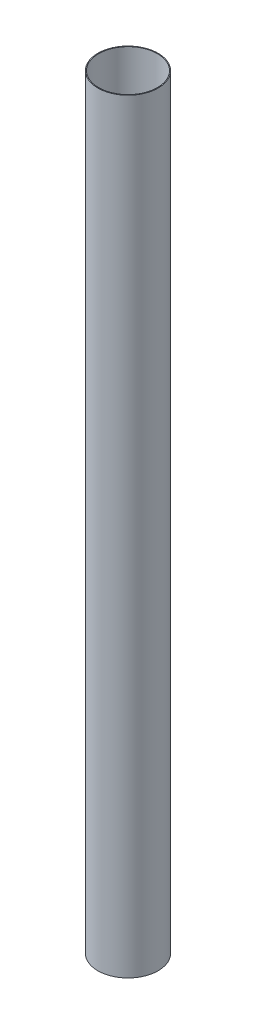
SolidWorks part; units mm, degrees
material "Hexcel AS4C (3000 Filaments)"
ref_plane "Front Plane" through (0, 0, 0) normal (0, 0, 1) x (1, 0, 0)
ref_plane "Top Plane" through (0, 0, 0) normal (0, 1, 0) x (1, 0, 0)
ref_plane "Right Plane" through (0, 0, 0) normal (1, 0, 0) x (0, 0, -1)
sketch "Sketch1" plane through (0, 0, 0) normal (0, 1, 0) x (1, 0, 0)
  circle A0 centre (0, 0) radius 63.5
  circle A1 centre (0, 0) radius 65.151
  dimension "D1" = 127
  dimension "D2" = 130.302
extrude "Boss-Extrude1" add sketch "Sketch1" along normal blind 1651
